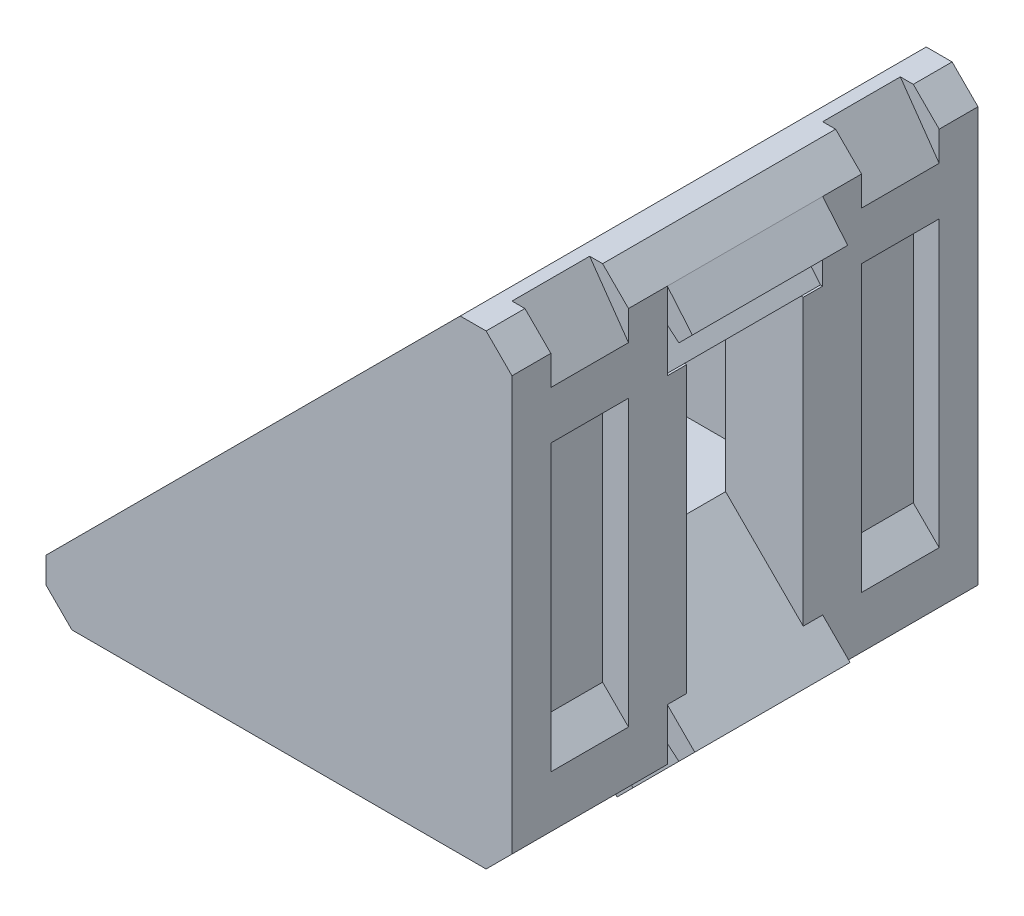
SolidWorks part; units mm, degrees
ref_plane "前视基准面" through (0, 0, 0) normal (0, 0, 1) x (1, 0, 0)
ref_plane "上视基准面" through (0, 0, 0) normal (0, 1, 0) x (1, 0, 0)
ref_plane "右视基准面" through (0, 0, 0) normal (1, 0, 0) x (0, 0, -1)
sketch "草图1" plane through (0, 0, 0) normal (0, 0, 1) x (1, 0, 0)
  line L3 (18.245, 55.2693) -> (18.1454, 55.3529)
  line L12 (32.5918, 56.5943) -> (33.2061, 57.2086)
  line L13 (33.2061, 57.2086) -> (29.1454, 61.2693)
  line L14 (29.1454, 61.2693) -> (29.1454, 58.2693)
  line L15 (29.1454, 58.2693) -> (26.1454, 58.2693)
  line L16 (26.1454, 58.2693) -> (30.2061, 54.2086)
  line L17 (30.2061, 54.2086) -> (30.8204, 54.8229)
  line L18 (30.8204, 54.8229) -> (29.8525, 55.9764)
  line L19 (29.8525, 55.9764) -> (31.4383, 57.5622)
  line L20 (31.4383, 57.5622) -> (32.5918, 56.5943)
  line L21 (18.1454, 55.3529) -> (18.1454, 58.2693)
  line L22 (18.1454, 58.2693) -> (15.1454, 58.2693)
  line L23 (15.1454, 58.2693) -> (14.1454, 57.2693)
  line L24 (14.1454, 57.2693) -> (14.1454, 56.2693)
  line L25 (14.1454, 56.2693) -> (15.1454, 55.2693)
  line L26 (15.1454, 55.2693) -> (16.2989, 54.3014)
  line L27 (16.2989, 54.3014) -> (16.8204, 54.8229)
  line L28 (16.8204, 54.8229) -> (15.8525, 55.9764)
  line L29 (15.8525, 55.9764) -> (16.5596, 56.6835)
  line L30 (16.5596, 56.6835) -> (18.1454, 55.3529)
  line L31 (31.4383, 71.5622) -> (32.5918, 70.5943)
  line L32 (32.5918, 70.5943) -> (33.1133, 71.1158)
  line L33 (33.1133, 71.1158) -> (32.1454, 72.2693)
  line L34 (32.1454, 72.2693) -> (31.1454, 73.2693)
  line L35 (31.1454, 73.2693) -> (30.1454, 73.2693)
  line L36 (30.1454, 73.2693) -> (29.1454, 72.2693)
  line L37 (29.1454, 72.2693) -> (29.1454, 69.2693)
  line L38 (29.1454, 69.2693) -> (32.0618, 69.2693)
  line L39 (32.0618, 69.2693) -> (30.7312, 70.8551)
  line L40 (30.7312, 70.8551) -> (31.4383, 71.5622)
extrude "拉伸1" add sketch "草图1" along normal blind 6
sketch "草图2" plane through (0, 0, 6) normal (0, 0, 1) x (1, 0, 0)
  line L0 (31.1454, 73.2693) -> (30.1454, 73.2693) construction
  line L1 (30.1454, 73.2693) -> (31.1454, 73.2693)
  line L2 (31.1454, 73.2693) -> (32.1454, 72.2693)
  line L3 (32.1454, 72.2693) -> (32.1454, 55.2693)
  line L4 (30.1454, 73.2693) -> (29.1454, 72.2693)
  line L5 (29.1454, 72.2693) -> (29.1454, 58.2693)
  line L6 (29.1454, 58.2693) -> (15.1454, 58.2693)
  line L7 (15.1454, 58.2693) -> (14.1454, 57.2693)
  line L8 (14.1454, 57.2693) -> (14.1454, 56.2693)
  line L9 (14.1454, 56.2693) -> (15.1454, 55.2693)
  line L10 (15.1454, 55.2693) -> (32.1454, 55.2693)
extrude "拉伸2" add sketch "草图2" along normal blind 4
ref_plane "基准面4" through (0, 0, 3) normal (0, 0, -1) x (-1, 0, 0)
mirror "镜向1" about plane through (0, 0, 3) normal (0, 0, -1) of "拉伸2"
sketch "草图3" plane through (0, 0, 10) normal (0, 0, 1) x (1, 0, 0)
  line L0 (30.1454, 73.2693) -> (31.1454, 73.2693)
  line L1 (31.1454, 73.2693) -> (32.1454, 72.2693)
  line L2 (32.1454, 72.2693) -> (32.1454, 55.2693)
  line L3 (32.1454, 55.2693) -> (15.1454, 55.2693)
  line L4 (15.1454, 55.2693) -> (14.1454, 56.2693)
  line L5 (14.1454, 56.2693) -> (14.1454, 57.2693)
  line L6 (14.1454, 57.2693) -> (30.1454, 73.2693)
extrude "拉伸3" add sketch "草图3" along normal blind 2
mirror "镜向2" about plane through (0, 0, 3) normal (0, 0, -1) of "拉伸3"
sketch "草图4" plane through (0, 0, 0) normal (0, 0, 1) x (1, 0, 0)
  line L0 (29.1454, 69.2693) -> (32.1454, 69.2693)
  line L1 (32.1454, 58.2693) -> (32.1454, 70.9688) construction
  line L2 (32.1454, 69.2693) -> (32.1454, 58.2693)
  line L3 (32.1454, 58.2693) -> (29.1454, 61.2693)
  line L4 (29.1454, 61.2693) -> (29.1454, 69.2693)
extrude "拉伸4" add sketch "草图4" along normal blind 0.75
mirror "镜向3" about plane through (0, 0, 3) normal (0, 0, -1) of "拉伸4"
sketch "草图5" plane through (0, 0, 0) normal (0, 0, 1) x (1, 0, 0)
  line L0 (26.1454, 58.2693) -> (18.1454, 58.2693)
  line L1 (18.1454, 58.2693) -> (18.1454, 55.2693)
  line L2 (16.4459, 55.2693) -> (29.1454, 55.2693) construction
  line L3 (18.1454, 55.2693) -> (29.1454, 55.2693)
  line L4 (29.1454, 55.2693) -> (26.1454, 58.2693)
extrude "拉伸5" add sketch "草图5" along normal blind 0.75
mirror "镜向4" about plane through (0, 0, 3) normal (0, 0, -1) of "拉伸5"
ref_plane "基准面5" through (0, 0, -4.5) normal (0, 0, -1) x (-1, 0, 0)
sketch "草图7" plane through (0, 0, -4.5) normal (0, 0, -1) x (-1, 0, 0)
  line L0 (-32.1454, 69.2693) -> (-31.1454, 69.2693)
  line L3 (-32.1454, 69.2693) -> (-32.1454, 58.2693)
  line L4 (-31.1454, 69.2693) -> (-31.1454, 59.2693)
  line L5 (-32.1454, 58.2693) -> (-31.1454, 59.2693)
  line L6 (-31.1454, 59.2693) -> (-31.1555, 59.3348)
  dimension "D1" = 1
  dimension "D2" = 10
extrude "切除-拉伸2" cut sketch "草图7" against normal blind 3 contours L4 L0 L3 L5
sketch "草图8" plane through (0, 0, -4.5) normal (0, 0, -1) x (-1, 0, 0)
  line L0 (-18.1454, 55.2693) -> (-18.1454, 56.2693)
  line L3 (-15.1454, 55.2693) -> (-32.1454, 55.2693) construction
  line L4 (-18.1454, 55.2693) -> (-29.1454, 55.2693)
  line L5 (-18.1454, 56.2693) -> (-28.1454, 56.2693)
  line L6 (-28.1454, 56.2693) -> (-29.1454, 55.2693)
  dimension "D2" = 1
  dimension "D3" = 10
extrude "切除-拉伸3" cut sketch "草图8" against normal blind 3
mirror "镜向5" about plane through (0, 0, 3) normal (0, 0, -1) of "切除-拉伸3", "切除-拉伸2"
sketch "草图9" plane through (0, 0, -4.5) normal (0, 0, -1) x (-1, 0, 0)
  line L0 (-30.6454, 73.2693) -> (-32.1454, 71.1271)
  line L2 (-30.6454, 73.2693) -> (-31.1454, 73.2693)
  line L3 (-31.1454, 73.2693) -> (-32.1454, 72.2693)
  line L4 (-32.1454, 72.2693) -> (-32.1454, 71.1271)
  dimension "D1" = 1.5
  dimension "D2" = 35
extrude "切除-拉伸4" cut sketch "草图9" against normal blind 3
sketch "草图10" plane through (0, 0, -4.5) normal (0, 0, -1) x (-1, 0, 0)
  line L0 (-14.1454, 56.7693) -> (-16.2876, 55.2693)
  line L1 (-14.1454, 57.2693) -> (-14.1454, 56.2693) construction
  line L2 (-15.1454, 55.2693) -> (-32.1454, 55.2693) construction
  line L3 (-16.2876, 55.2693) -> (-15.1454, 55.2693)
  line L4 (-15.1454, 55.2693) -> (-14.1454, 56.2693)
  line L5 (-14.1454, 56.2693) -> (-14.1454, 56.7693)
  dimension "D1" = 1.5
  dimension "D2" = 55
extrude "切除-拉伸5" cut sketch "草图10" against normal blind 3
mirror "镜向6" about plane through (0, 0, 3) normal (0, 0, -1) of "切除-拉伸4", "切除-拉伸5"
chamfer "倒角1" distance 1 angle 45 2 edges at (32.1454, 55.2693, -3) (32.1454, 55.2693, 9)
